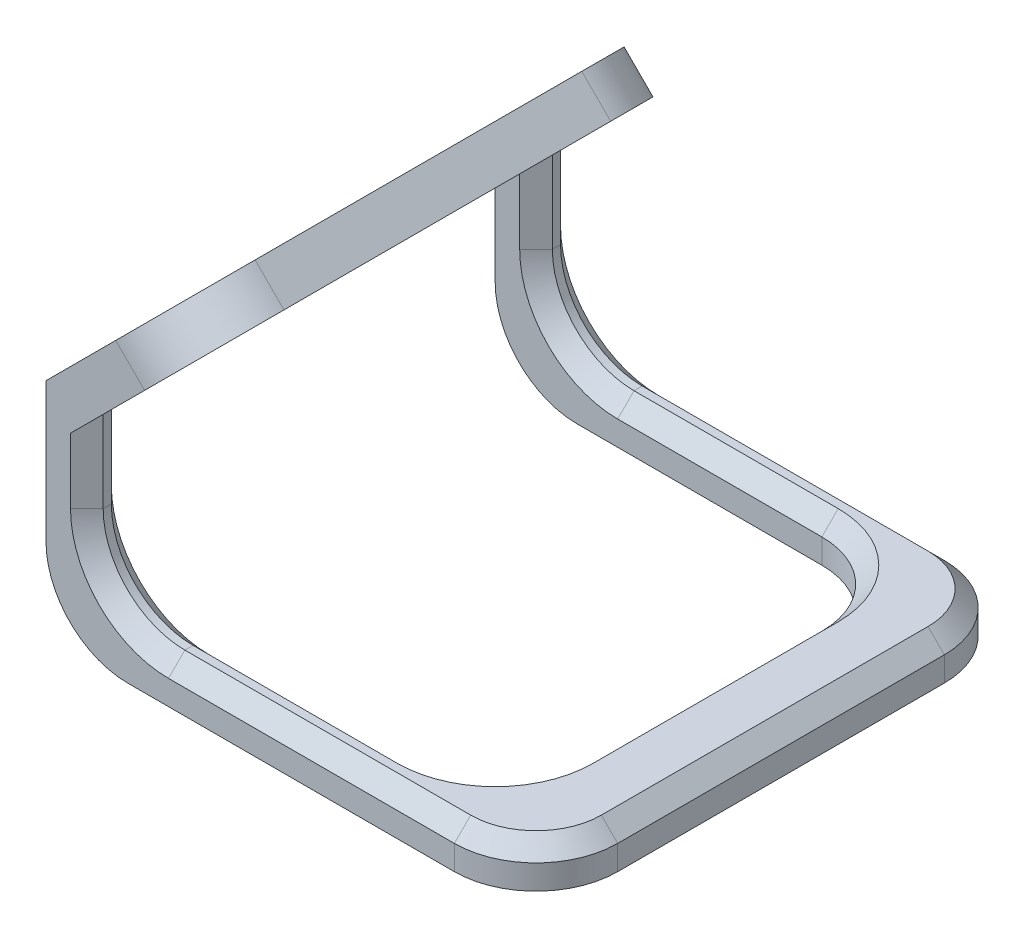
SolidWorks part; units mm, degrees
material "1060 Alloy"
ref_plane "Front Plane" through (0, 0, 0) normal (0, 0, 1) x (1, 0, 0)
ref_plane "Top Plane" through (0, 0, 0) normal (0, 1, 0) x (1, 0, 0)
ref_plane "Right Plane" through (0, 0, 0) normal (1, 0, 0) x (0, 0, -1)
sketch "Sketch1" plane through (0, 0, 0) normal (0, 0, 1) x (1, 0, 0)
  line L0 (0, 0) -> (-60, 0)
  line L1 (-60, 0) -> (-60, 27.0711)
  line L2 (-60, 27.0711) -> (-44.3934, 42.6777)
  line L4 (0, 0) -> (0, 5)
  line L5 (0, 5) -> (-55, 5)
  line L6 (-55, 5) -> (-55, 25)
  line L7 (-55, 25) -> (-40.8579, 39.1421)
  line L8 (-40.8579, 39.1421) -> (-44.3934, 42.6777)
  point P0 (-60, 27.0082)
  point P9 (18.7172, 0)
  dimension "D1" = 135
  dimension "D2" = 5
  dimension "D3" = 5
  dimension "D4" = 60
  dimension "D5" = 5
  dimension "D6" = 20
  dimension "D7" = 20
extrude "Boss-Extrude1" add sketch "Sketch1" along normal blind 60
sketch "Sketch2" plane through (-60, 0, 0) normal (-1, 0, 0) x (0, 0, 1)
  line L0 (60, 0) -> (0, 0) construction
  line L1 (5, 0) -> (55, 0)
  line L2 (5, 0) -> (5, 27.0711)
  line L3 (5, 27.0711) -> (55, 27.0711)
  line L4 (55, 0) -> (55, 27.0711)
  line L5 (60, 27.0711) -> (60, 0) construction
  line L6 (0, 27.0711) -> (0, 0) construction
  line L8 (60, 27.0711) -> (0, 27.0711) construction
  point P10 (55, 25.4459)
  point P11 (0, 0)
  dimension "D1" = 5
  dimension "D2" = 5
extrude "Cut-Extrude1" cut sketch "Sketch2" against normal blind 50
fillet "Fillet1" radius 10 10 edges at (-10, 2.5, 5) (-10, 2.5, 55) (-60, 0, 2.5) (-60, 0, 57.5) (0, 2.5, 0) (0, 2.5, 60) (-55, 5, 2.5) (-55, 5, 57.5) (-42.6256, 40.9099, 60) (-42.6256, 40.9099, 0)
chamfer "Chamfer1" distance 2 angle 45 18 edges at (-55, 20, 0) (-52.0711, 7.9289, 0) (-27.5, 5, 0) (-2.9289, 5, 2.9289) (0, 5, 30) (-55, 20, 60) (-2.9289, 5, 57.0711) (-52.0711, 7.9289, 60) (-27.5, 5, 60) (-55, 20, 5) (-55, 20, 55) (-52.0711, 7.9289, 5) (-52.0711, 7.9289, 55) (-32.5, 5, 5) (-32.5, 5, 55) (-12.9289, 5, 7.9289) (-12.9289, 5, 52.0711) (-10, 5, 30)
sketch "Sketch3" plane through (-43.5355, 43.5355, 0) normal (-0.7071, 0.7071, 0) x (0, 0, 1)
  line L0 (30, -23.2843) -> (30, -1.2132) construction
  line L1 (55, -23.2843) -> (5, -23.2843) construction
  line L2 (50, -1.2132) -> (10, -1.2132) construction
  circle A5 centre (30, -6.2843) radius 2
  circle A6 centre (36, -12.2843) radius 2
  circle A7 centre (24, -12.2843) radius 2
  circle A8 centre (18, -6.2843) radius 2
  circle A9 centre (12, -12.2843) radius 2
  circle A10 centre (42, -6.2843) radius 2
  circle A11 centre (48, -12.2843) radius 2
  point P20 (0, 0)
  point P21 (0, 0)
  point P22 (0, 0)
  point P23 (0, 0)
  point P24 (0, 0)
  point P25 (39.5398, -7.972)
  dimension "D1" = 4
  dimension "D2" = 6
  dimension "D3" = 6
  dimension "D4" = 6
  dimension "D5" = 12
  dimension "D6" = 12
  dimension "D7" = 12
  dimension "D8" = 12
  dimension "D9" = 17
extrude "Cut-Extrude2" cut sketch "Sketch3" against normal blind 30
chamfer "Chamfer2" distance 5 angle 45 1 edges at (-60, 27.0711, 30)
